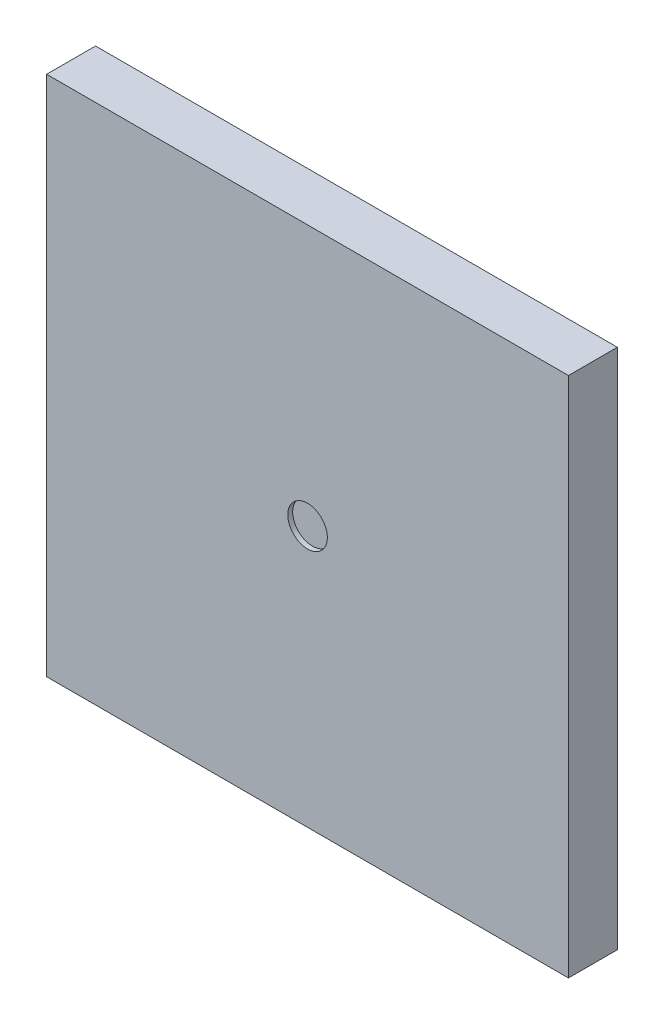
SolidWorks part; units mm, degrees
ref_plane "Front Plane" through (0, 0, 0) normal (0, 0, 1) x (1, 0, 0)
ref_plane "Top Plane" through (0, 0, 0) normal (0, 1, 0) x (1, 0, 0)
ref_plane "Right Plane" through (0, 0, 0) normal (1, 0, 0) x (0, 0, -1)
sketch "Sketch1" plane through (0, 0, 0) normal (0, 0, 1) x (1, 0, 0)
  line L0 (13.55, 0) -> (-13.55, 0) construction
  line L1 (-13.55, 13.55) -> (13.55, 13.55)
  line L2 (-13.55, 13.55) -> (-13.55, -13.55)
  line L3 (-13.55, -13.55) -> (13.55, -13.55)
  line L4 (13.55, 13.55) -> (13.55, -13.55)
  line L5 (0, 13.55) -> (0, -13.55) construction
  dimension "D1" = 27.1
  dimension "D2" = 27.1
extrude "Extrude1" add sketch "Sketch1" along normal blind 2.54
sketch "Sketch2" plane through (0, 0, 2.54) normal (0, 0, 1) x (1, 0, 0)
  circle A0 centre (0, 0) radius 1.0282
extrude "Cut-Extrude1" cut sketch "Sketch2" against normal blind 0.254
